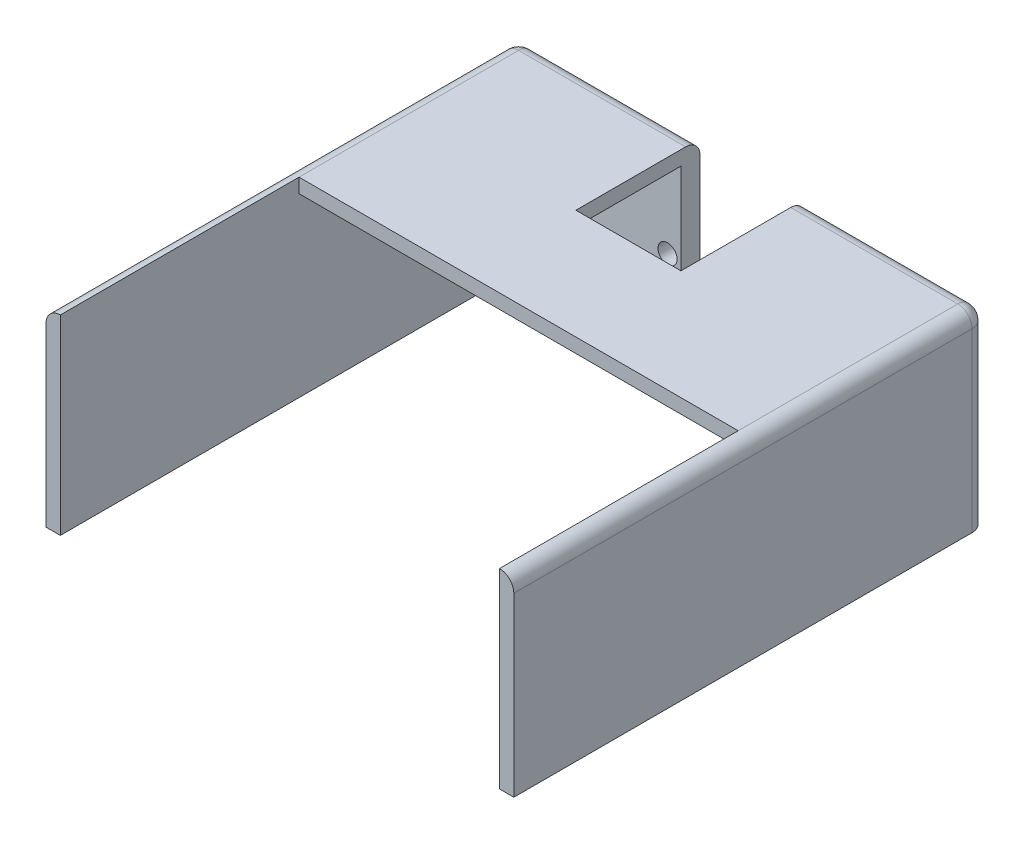
SolidWorks part; units mm, degrees
ref_plane "Alzado" through (0, 0, 0) normal (0, 0, 1) x (1, 0, 0)
ref_plane "Planta" through (0, 0, 0) normal (0, 1, 0) x (1, 0, 0)
ref_plane "Vista lateral" through (0, 0, 0) normal (1, 0, 0) x (0, 0, -1)
sketch "Croquis2" plane through (0, 0, 0) normal (0, 0, 1) x (1, 0, 0)
  line L1 (-49, -20) -> (49, -20)
  line L2 (-49, -20) -> (-49, 20)
  line L3 (-49, 20) -> (49, 20)
  line L4 (49, -20) -> (49, 20)
  line L5 (-49, -20) -> (49, 20) construction
  line L6 (-49, 20) -> (49, -20) construction
  line L7 (-49, -20) -> (-46, -20)
  line L8 (-49, -20) -> (-49, 20)
  line L9 (-49, 20) -> (-46, 20)
  line L10 (-46, -20) -> (-46, 20)
  line L11 (-49, -20) -> (-46, 20) construction
  line L12 (-49, 20) -> (-46, -20) construction
  line L13 (49, -20) -> (46, -20)
  line L14 (49, -20) -> (49, 20)
  line L15 (49, 20) -> (46, 20)
  line L16 (46, -20) -> (46, 20)
  line L17 (-46, -20) -> (46, -20)
  line L18 (-46, -20) -> (-46, 20)
  line L19 (-46, 20) -> (46, 20)
  line L20 (46, -20) -> (46, 20)
  line L21 (-46, -20) -> (46, 20) construction
  line L22 (-46, 20) -> (46, -20) construction
  point P0 (0, 0)
  point P6 (-47.5, 0)
  point P13 (0, 0)
  dimension "D1" = 98
  dimension "D2" = 40
  dimension "D3" = 3
  dimension "D4" = 3
extrude "Saliente-Extruir2" add sketch "Croquis2" along normal blind 4 contours L1 L16 L3 L10
sketch "Croquis3" plane through (0, 0, 4) normal (0, 0, 1) x (1, 0, 0)
  line L1 (-49, -20) -> (-46, -20)
  line L2 (-49, -20) -> (-49, 20)
  line L3 (-49, 20) -> (-46, 20)
  line L4 (-46, -20) -> (-46, 20)
  line L5 (-49, -20) -> (-46, 20) construction
  line L6 (-49, 20) -> (-46, -20) construction
  line L7 (49, -20) -> (46, -20)
  line L8 (49, -20) -> (49, 20)
  line L9 (49, 20) -> (46, 20)
  line L10 (46, -20) -> (46, 20)
  point P0 (-47.5, 0)
extrude "Saliente-Extruir3" add sketch "Croquis3" along normal blind 95 separate body
sketch "Croquis4" plane through (0, 0, 4) normal (0, 0, -1) x (-1, 0, 0)
  line L1 (-46, 20) -> (-49, 20)
  line L2 (-46, 20) -> (-46, -20)
  line L3 (-46, -20) -> (-49, -20)
  line L4 (-49, 20) -> (-49, -20)
  line L5 (46, 20) -> (49, 20)
  line L6 (46, 20) -> (46, -20)
  line L7 (46, -20) -> (49, -20)
  line L8 (49, 20) -> (49, -20)
extrude "Saliente-Extruir4" add sketch "Croquis4" along normal blind 4
fillet "Redondeo1" radius 3 2 edges at (-49, 0, 0) (49, 0, 0)
sketch "Croquis5" plane through (0, 0, 4) normal (0, 0, 1) x (1, 0, 0)
  line L0 (46, -20) -> (46, 20) construction
  line L1 (-46, 20) -> (46, 20)
  line L2 (-46, 20) -> (-46, 17)
  line L3 (-46, 17) -> (46, 17)
  line L4 (46, 20) -> (46, 17)
  dimension "D1" = 3
extrude "Saliente-Extruir5" add sketch "Croquis5" along normal blind 45
fillet "Redondeo2" radius 3 5 edges at (-48.1213, 20, 0.8787) (0, 20, 0) (48.1213, 20, 0.8787) (-49, 20, 51) (49, 20, 51)
sketch "Croquis6" plane through (0, 0, 0) normal (0, 0, -1) x (-1, 0, 0)
  line L0 (0, 0) -> (0, -20) construction
  line L1 (49, -20) -> (-49, -20) construction
  line L2 (0, -20) -> (0, 17) construction
  line L5 (-11, 20) -> (11, 20)
  line L6 (-11, 20) -> (-11, -10)
  line L7 (-11, -10) -> (11, -10)
  line L8 (11, 20) -> (11, -10)
  line L10 (49, 20) -> (-49, 20) construction
  dimension "D1" = 22
  dimension "D2" = 11
  dimension "D3" = 30
extrude "Cortar-Extruir1" cut sketch "Croquis6" against normal blind 26
sketch "Croquis7" plane through (0, 0, 0) normal (0, 0, -1) x (-1, 0, 0)
  line L0 (-11, -10) -> (11, -10) construction
  line L2 (49, -20) -> (-49, -20) construction
  line L3 (0, 5.9093) -> (0, -22.5342) construction
  line L4 (11, -10) -> (11, 17) construction
  circle A0 centre (5, -15) radius 2
  circle A1 centre (-5, -15) radius 2
  circle A2 centre (13.7336, -10.3) radius 2
  circle A3 centre (-13.7336, -10.3) radius 2
  circle A4 centre (13.8, -0.3002) radius 2
  circle A5 centre (-13.8, -0.3002) radius 2
  dimension "D3" = 4
  dimension "D4" = 6
  dimension "D6" = 4
  dimension "D1" = 6
  dimension "D2" = 5
  dimension "D5" = 5
  dimension "D7" = 2.75
  dimension "D8" = 9.7
  dimension "D9" = 10
  dimension "D10" = 2.8
extrude "Cortar-Extruir2" cut sketch "Croquis7" against normal blind 10
